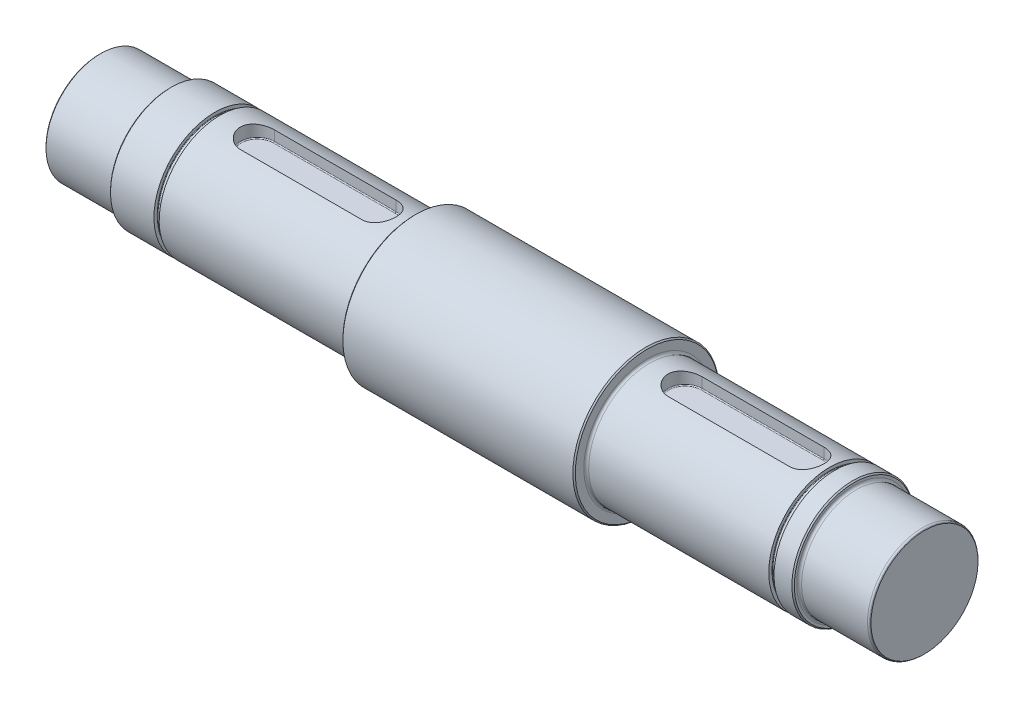
SolidWorks part; units mm, degrees
material "AISI 1045 Steel, cold drawn"
ref_plane "Front Plane" through (0, 0, 0) normal (0, 0, 1) x (1, 0, 0)
ref_plane "Top Plane" through (0, 0, 0) normal (0, 1, 0) x (1, 0, 0)
ref_plane "Right Plane" through (0, 0, 0) normal (1, 0, 0) x (0, 0, -1)
sketch "Sketch1" plane through (0, 0, 0) normal (0, 0, 1) x (1, 0, 0)
  line L0 (-187.5976, 22.5) -> (-187.5976, 45)
  line L1 (-187.5976, 45) -> (-158.5976, 45)
  line L2 (-158.5976, 45) -> (-158.5976, 47.5)
  line L3 (-158.5976, 47.5) -> (-140.2476, 47.5)
  line L4 (-58.0976, 47.5) -> (-58.0976, 52.5)
  line L5 (-58.0976, 52.5) -> (37.4024, 52.5)
  line L6 (37.4024, 52.5) -> (37.4024, 47.5)
  line L7 (37.4024, 47.5) -> (112.4024, 47.5)
  line L8 (122.4024, 47.5) -> (122.4024, 45)
  line L9 (122.4024, 45) -> (151.4024, 45)
  line L10 (151.4024, 45) -> (151.4024, 22.5)
  line L11 (151.4024, 22.5) -> (-187.5976, 22.5)
  line L12 (-140.2476, 47.5) -> (-140.2476, 46)
  line L13 (-140.2476, 46) -> (-138.0976, 46)
  line L14 (-138.0976, 46) -> (-138.0976, 47.5)
  line L15 (-138.0976, 47.5) -> (-58.0976, 47.5)
  line L16 (114.5524, 47.5) -> (114.5524, 46)
  line L17 (114.5524, 46) -> (112.4024, 46)
  line L18 (112.4024, 46) -> (112.4024, 47.5)
  line L19 (114.5524, 47.5) -> (122.4024, 47.5)
  point P14 (-140.2476, 46.75)
  dimension "D1" = 22.5
  dimension "D2" = 29
  dimension "D3" = 100.5
  dimension "D4" = 95.5
  dimension "D5" = 85
  dimension "D6" = 29
  dimension "D7" = 25
  dimension "D8" = 30
  dimension "D9" = 25
  dimension "D10" = 22.5
  dimension "D11" = 20.5
  dimension "D12" = 2.15
  dimension "D13" = 1.5
  dimension "D14" = 10
  dimension "D15" = 2.15
  dimension "D16" = 1.5
revolve "Revolve1" add sketch "Sketch1" angle 360 about L11
fillet "Fillet1" radius 0.2 4 edges at (112.4024, 46, 0) (114.5524, 46, 0) (-138.0976, 46, 0) (-140.2476, 46, 0)
ref_plane "Plane1" through (0, 47.5, 0) normal (0, 1, 0) x (1, 0, 0)
ref_plane "Plane2" through (0, 47.5, 0) normal (0, 1, 0) x (1, 0, 0)
sketch "Sketch2" plane through (0, 47.5, 0) normal (0, 1, 0) x (1, 0, 0)
  line L0 (-72.7519, 0) -> (-122.7519, 0) construction
  line L1 (-72.7519, -7) -> (-122.7519, -7)
  line L2 (-72.7519, 7) -> (-122.7519, 7)
  arc A0 (-72.7519, -7) -> (-72.7519, 7) centre (-72.7519, 0) ccw
  arc A1 (-122.7519, 7) -> (-122.7519, -7) centre (-122.7519, 0) ccw
  point P3 (-97.7519, 0)
  dimension "D1" = 50
  dimension "D2" = 14
sketch "Sketch3" plane through (0, 47.5, 0) normal (0, 1, 0) x (1, 0, 0)
  line L0 (103.0394, 0) -> (53.0394, 0) construction
  line L1 (103.0394, -7) -> (53.0394, -7)
  line L2 (103.0394, 7) -> (53.0394, 7)
  line L3 (112.4024, 0) -> (83.7347, 0) construction
  line L4 (112.4024, -23.7) -> (112.4024, 23.7) construction
  arc A0 (103.0394, -7) -> (103.0394, 7) centre (103.0394, 0) ccw
  arc A1 (53.0394, 7) -> (53.0394, -7) centre (53.0394, 0) ccw
  point P2 (78.0394, 0)
  dimension "D1" = 50
  dimension "D2" = 14
extrude "Cut-Extrude1" cut sketch "Sketch3" against normal blind 5.5
extrude "Cut-Extrude2" cut sketch "Sketch2" against normal blind 5.5 contours L1 A1 L2 A0
chamfer "Chamfer1" distance 0.5 angle 45 6 edges at (151.4024, 45, 0) (122.4024, 47.5, 0) (37.4024, 52.5, 0) (-58.0976, 52.5, 0) (-158.5976, 47.5, 0) (-187.5976, 45, 0)
fillet "Fillet2" radius 1 5 edges at (122.4024, 45, 0) (150.9024, 22.5, -22.5) (37.4024, 47.5, 0) (-58.0976, 47.5, 0) (-158.5976, 45, 0)
fillet "Fillet3" radius 0.4 8 edges at (110.0394, 42, 0) (78.0394, 42, 7) (46.0394, 42, 0) (-65.7519, 42, 0) (-97.7519, 42, 7) (-129.7519, 42, 0) (78.0394, 42, -7) (-97.7519, 42, -7)
equation "\"5.510.00mm\"=10"
